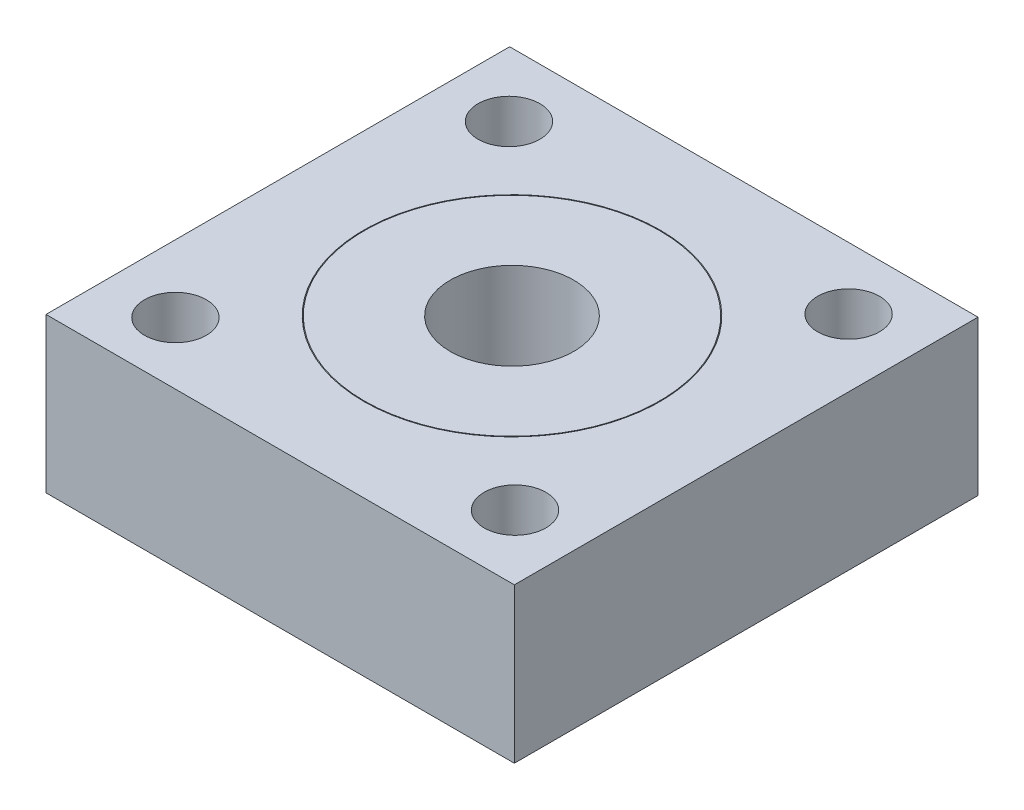
SolidWorks part; units mm, degrees
material "AISI 304"
ref_plane "Front Plane" through (0, 0, 0) normal (0, 0, 1) x (1, 0, 0)
ref_plane "Top Plane" through (0, 0, 0) normal (0, 1, 0) x (1, 0, 0)
ref_plane "Right Plane" through (0, 0, 0) normal (1, 0, 0) x (0, 0, -1)
sketch "Sketch1" plane through (0, 0, 0) normal (0, 1, 0) x (1, 0, 0)
  line L1 (-15.1537, 15.0013) -> (15.1537, 15.0013)
  line L2 (-15.1537, 15.0013) -> (-15.1537, -15.0013)
  line L3 (-15.1537, -15.0013) -> (15.1537, -15.0013)
  line L4 (15.1537, 15.0013) -> (15.1537, -15.0013)
  line L5 (-15.1537, 15.0013) -> (15.1537, -15.0013) construction
  line L6 (-15.1537, -15.0013) -> (15.1537, 15.0013) construction
  point P0 (0, 0)
extrude "Boss-Extrude1" add sketch "Sketch1" along normal blind 10
sketch "Sketch2" plane through (0, 10, 0) normal (0, 1, 0) x (1, 0, 0)
  circle A0 centre (0, 0) radius 9.55
  circle A1 centre (0, 0) radius 9.6
extrude "Cut-Extrude1" cut sketch "Sketch2" against normal blind 7
sketch "Sketch3" plane through (0, 10, 0) normal (0, 1, 0) x (1, 0, 0)
  circle A0 centre (0, 0) radius 4
extrude "Cut-Extrude2" cut sketch "Sketch3" against normal blind 10
sketch "Sketch4" plane through (0, 10, 0) normal (0, 1, 0) x (1, 0, 0)
  circle A0 centre (10.7923, 10.9875) radius 2
extrude "Cut-Extrude3" cut sketch "Sketch4" against normal blind 10
pattern_circular "CirPattern1" count 4 every 90 about axis through (0, 0, 0) along (0, 1, 0) of "Cut-Extrude3"
